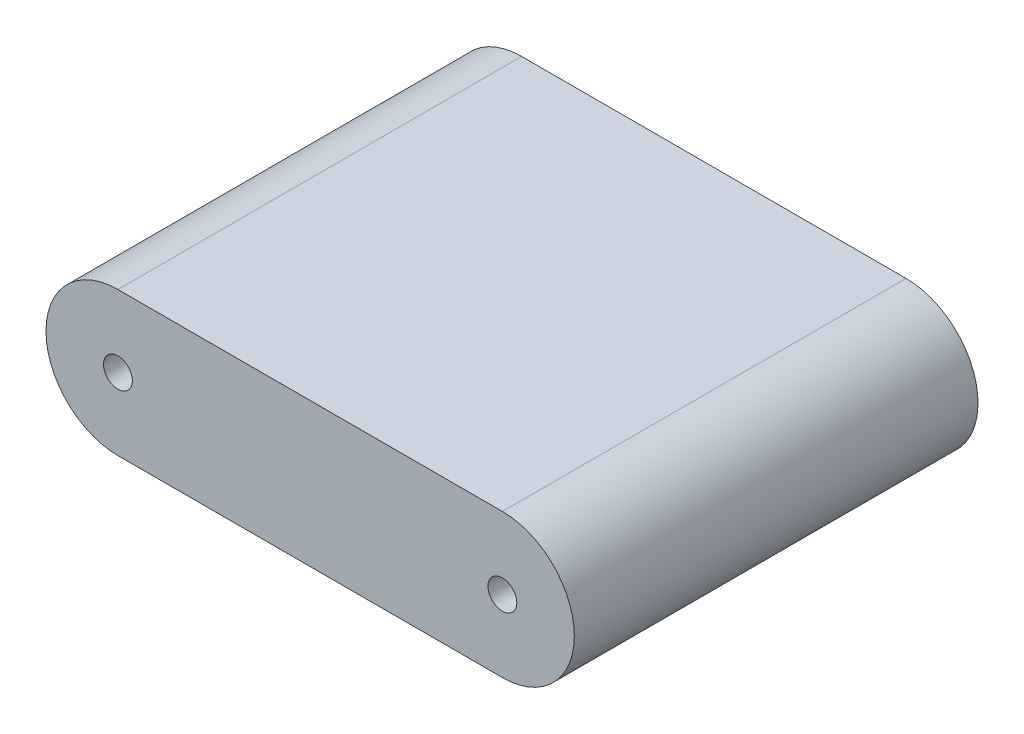
SolidWorks part; units mm, degrees
ref_plane "Front Plane" through (0, 0, 0) normal (0, 0, 1) x (1, 0, 0)
ref_plane "Top Plane" through (0, 0, 0) normal (0, 1, 0) x (1, 0, 0)
ref_plane "Right Plane" through (0, 0, 0) normal (1, 0, 0) x (0, 0, -1)
sketch "Sketch1" plane through (0, 0, 0) normal (0, 0, 1) x (1, 0, 0)
  line L0 (-20, 0) -> (20, 0) construction
  line L7 (-20, 7.4833) -> (20, 7.4833)
  line L8 (-20, -7.4833) -> (20, -7.4833)
  circle A0 centre (20, 0) radius 1.5
  circle A1 centre (-20, 0) radius 1.5
  arc A2 (-20, 7.4833) -> (-20, -7.4833) centre (-20, 0) ccw
  arc A3 (20, -7.4833) -> (20, 7.4833) centre (20, 0) ccw
  point P0 (0, 0)
  point P10 (0, 0)
extrude "Boss-Extrude1" add sketch "Sketch1" along normal blind 42
